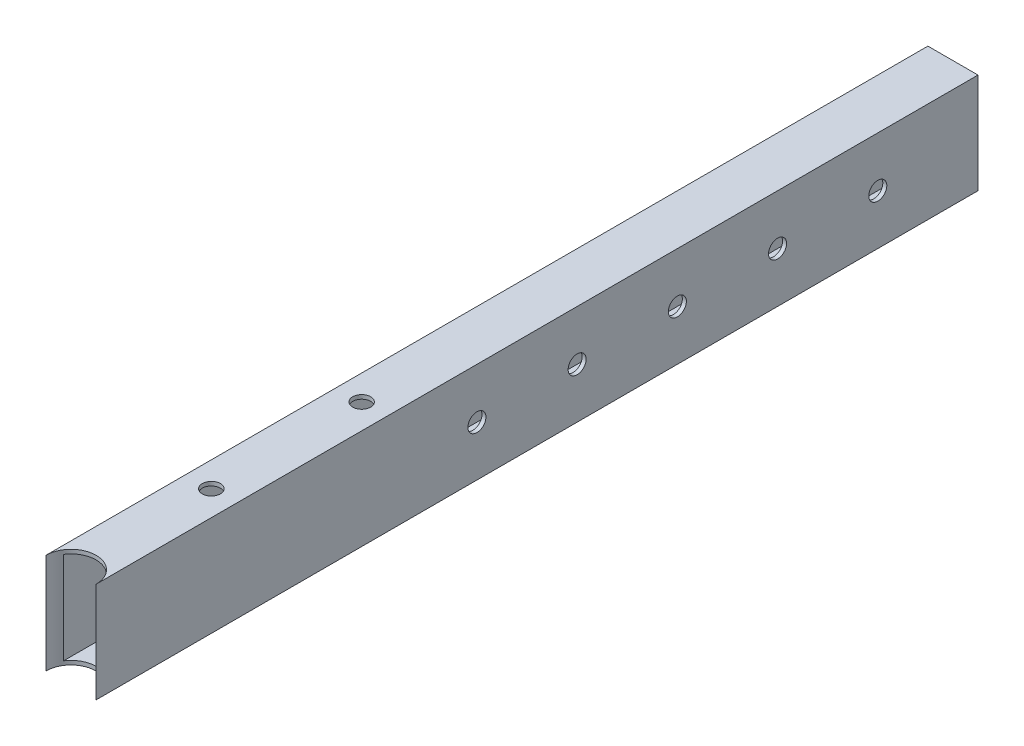
SolidWorks part; units mm, degrees
ref_plane "Спереди" through (0, 0, 0) normal (0, 0, 1) x (1, 0, 0)
ref_plane "Сверху" through (0, 0, 0) normal (0, 1, 0) x (1, 0, 0)
ref_plane "Справа" through (0, 0, 0) normal (1, 0, 0) x (0, 0, -1)
sketch "Эскиз1" plane through (0, 0, 0) normal (0, 0, 1) x (1, 0, 0)
  line L1 (-12.5, 25) -> (12.5, 25)
  line L2 (-12.5, 25) -> (-12.5, -25)
  line L3 (-12.5, -25) -> (12.5, -25)
  line L4 (12.5, 25) -> (12.5, -25)
  line L5 (-12.5, 25) -> (12.5, -25) construction
  line L6 (-12.5, -25) -> (12.5, 25) construction
  line L7 (-10.5, 23) -> (10.5, 23)
  line L8 (-10.5, 23) -> (-10.5, -23)
  line L9 (-10.5, -23) -> (10.5, -23)
  line L10 (10.5, 23) -> (10.5, -23)
  line L11 (-10.5, 23) -> (10.5, -23) construction
  line L12 (-10.5, -23) -> (10.5, 23) construction
  point P0 (0, 0)
  point P5 (0, 0)
  dimension "D1" = 25
  dimension "D2" = 50
  dimension "D3" = 2
  dimension "D4" = 2
extrude "Бобышка-Вытянуть1" add sketch "Эскиз1" along normal blind 440
sketch "Эскиз2" plane through (0, 25, 0) normal (0, 1, 0) x (1, 0, 0)
  line L0 (12.5, -440) -> (-12.5, -440) construction
  circle A0 centre (0, -440) radius 12.5
  circle A1 centre (0, -370) radius 4.5
  circle A2 centre (0, -295) radius 4.5
  dimension "D1" = 75
  dimension "D3" = 9
  dimension "D2" = 70
extrude "Вырез-Вытянуть1" cut sketch "Эскиз2" against normal blind 50
sketch "Эскиз3" plane through (12.5, 0, 0) normal (1, 0, 0) x (0, 0, -1)
  line L0 (-440, -25) -> (0, -25) construction
  line L1 (0, -25) -> (0, 25) construction
  circle A0 centre (-50, 0) radius 4.5
  circle A1 centre (-100, 0) radius 4.5
  circle A2 centre (-150, 0) radius 4.5
  circle A3 centre (-200, 0) radius 4.5
  circle A4 centre (-250, 0) radius 4.5
  dimension "D1" = 5
  dimension "D2" = 9
  dimension "D4" = 50
  dimension "D3" = 25
  dimension "D5" = 50
extrude "Вырез-Вытянуть2" cut sketch "Эскиз3" against normal blind 2
